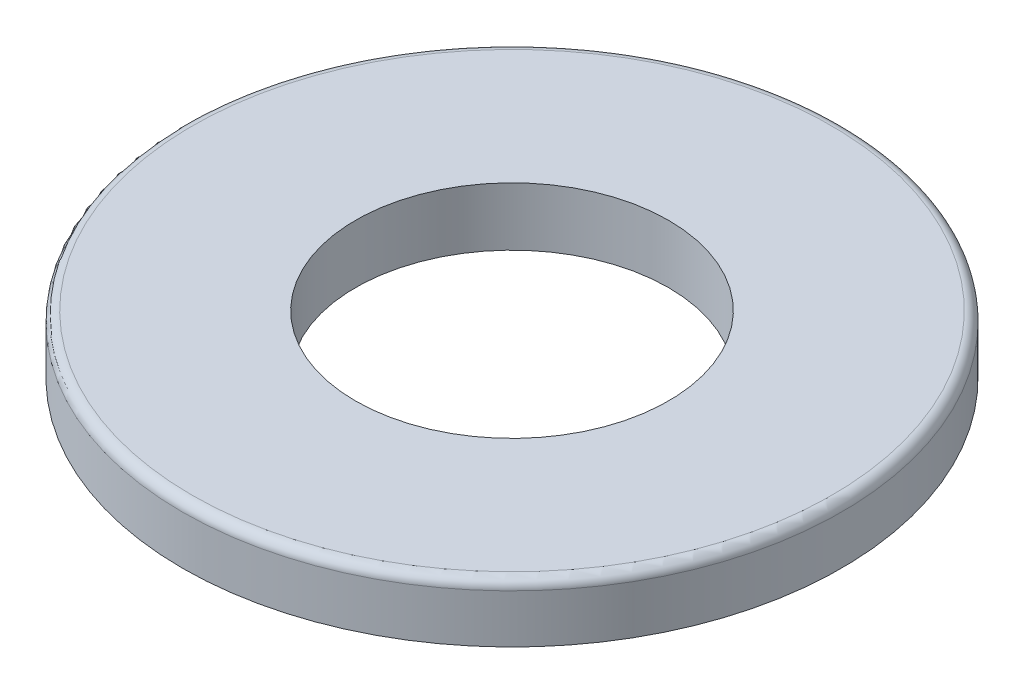
SolidWorks part; units mm, degrees
ref_plane "前视基准面" through (0, 0, 0) normal (0, 0, 1) x (1, 0, 0)
ref_plane "上视基准面" through (0, 0, 0) normal (0, 1, 0) x (1, 0, 0)
ref_plane "右视基准面" through (0, 0, 0) normal (1, 0, 0) x (0, 0, -1)
sketch "草图1" plane through (0, 0, 0) normal (0, 1, 0) x (1, 0, 0)
  circle A0 centre (0, 0) radius 16.95
  circle A1 centre (0, 0) radius 8.05
  dimension "D1" = 33.9
  dimension "D2" = 16.1
extrude "凸台-拉伸1" add sketch "草图1" along normal blind 3
fillet "圆角1" radius 0.5 1 edges at (0, 3, 16.95)
